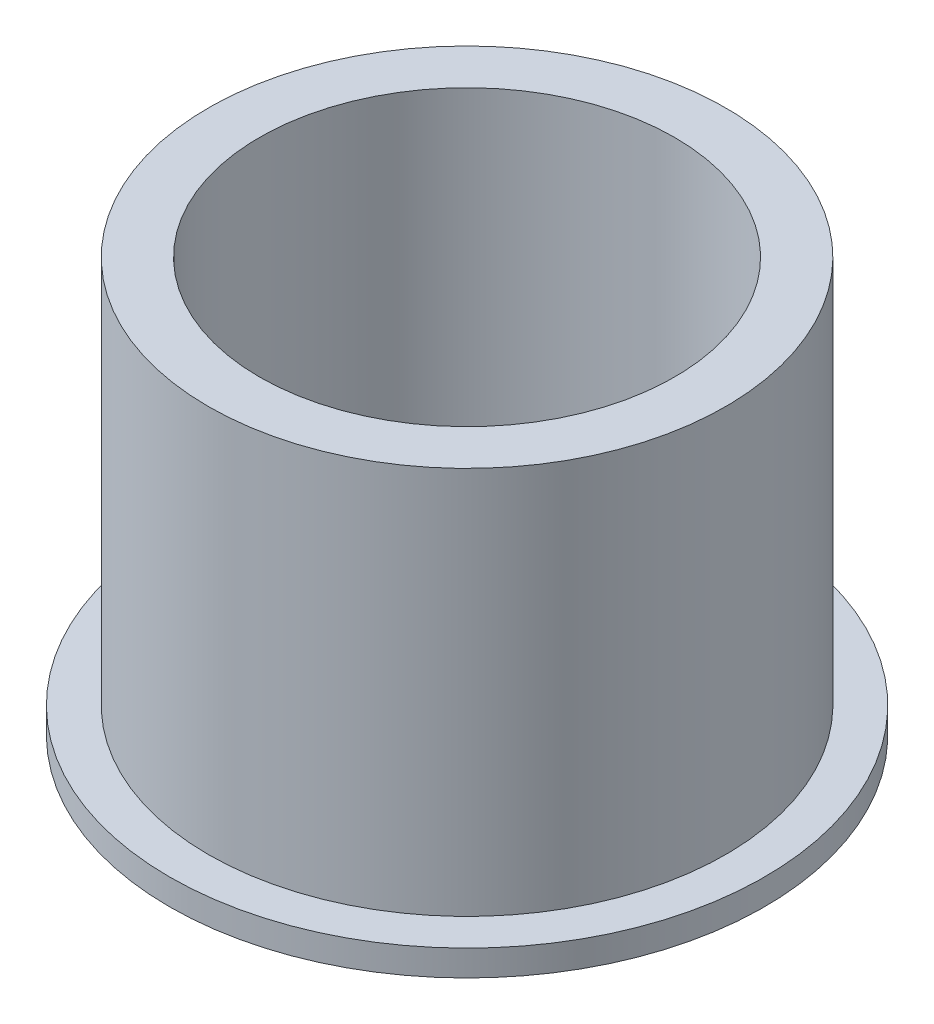
SolidWorks part; units mm, degrees
ref_plane "Front" through (0, 0, 0) normal (0, 0, 1) x (1, 0, 0)
ref_plane "Top" through (0, 0, 0) normal (0, 1, 0) x (1, 0, 0)
ref_plane "Right" through (0, 0, 0) normal (1, 0, 0) x (0, 0, -1)
sketch "Sketch1" plane through (0, 0, 0) normal (0, 1, 0) x (1, 0, 0)
  circle A0 centre (0, 0) radius 12.7381
  circle A1 centre (0, 0) radius 15.875
  circle A2 centre (0, 0) radius 18.2562
  dimension "ID" = 25.4762
  dimension "OD" = 31.75
  dimension "FlangeOD" = 36.5125
sketch "Sketch2" plane through (0, 0, 0) normal (0, 1, 0) x (1, 0, 0)
  circle A0 centre (0, 0) radius 12.7381 construction
  circle A1 centre (0, 0) radius 15.875 construction
  circle A2 centre (0, 0) radius 12.7381
  circle A3 centre (0, 0) radius 15.875
extrude "Boss-Extrude1" add sketch "Sketch2" along normal blind 25.4
sketch "Sketch3" plane through (0, 0, 0) normal (0, 1, 0) x (1, 0, 0)
  circle A0 centre (0, 0) radius 18.2562 construction
  circle A1 centre (0, 0) radius 15.875 construction
  circle A2 centre (0, 0) radius 18.2562
  circle A3 centre (0, 0) radius 15.875
extrude "Boss-Extrude2" add sketch "Sketch3" along normal blind 1.5875
